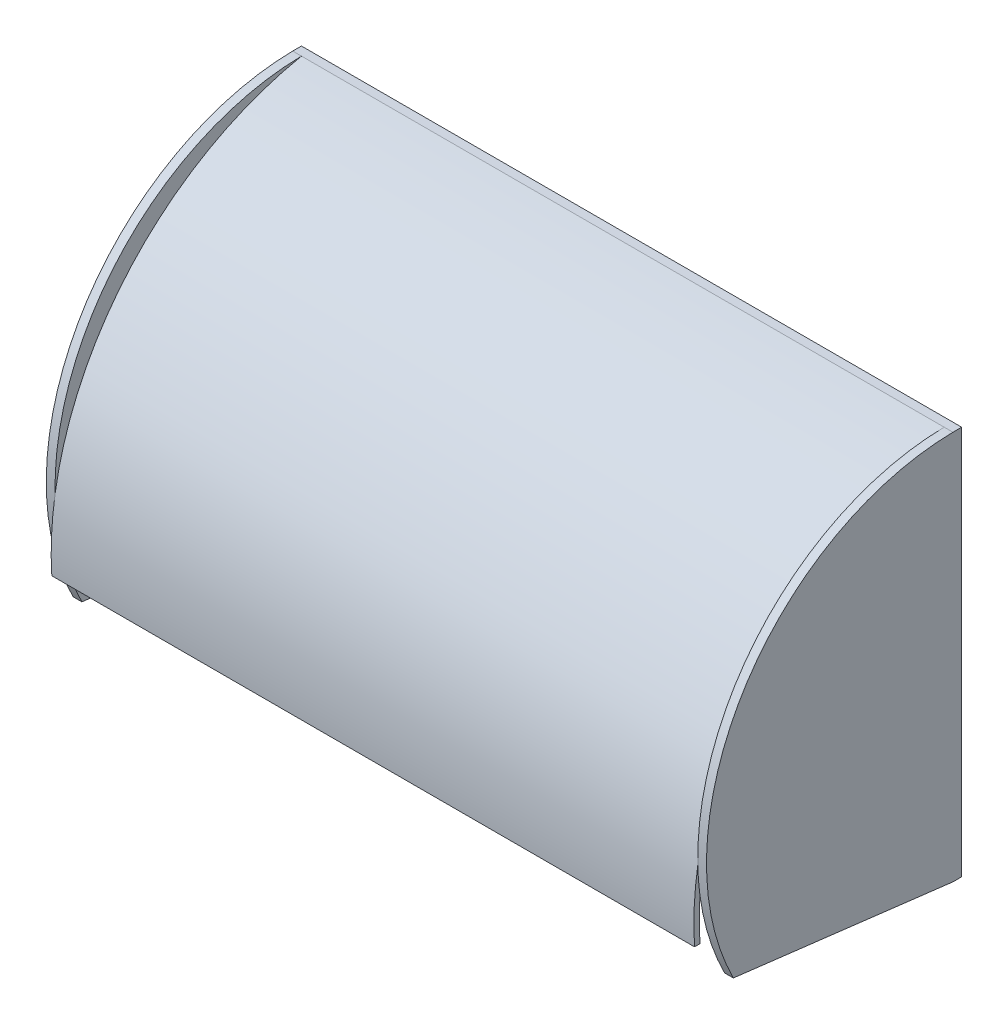
SolidWorks part; units mm, degrees
ref_plane "Front Plane" through (0, 0, 0) normal (0, 0, 1) x (1, 0, 0)
ref_plane "Top Plane" through (0, 0, 0) normal (0, 1, 0) x (1, 0, 0)
ref_plane "Right Plane" through (0, 0, 0) normal (1, 0, 0) x (0, 0, -1)
sketch "Sketch1" plane through (0, 0, 0) normal (0, 0, 1) x (1, 0, 0)
  line L1 (-93.3016, 56.5286) -> (93.3016, 56.5286)
  line L2 (-93.3016, 56.5286) -> (-93.3016, -56.5286)
  line L3 (-93.3016, -56.5286) -> (93.3016, -56.5286)
  line L4 (93.3016, 56.5286) -> (93.3016, -56.5286)
  line L5 (-93.3016, 56.5286) -> (93.3016, -56.5286) construction
  line L6 (-93.3016, -56.5286) -> (93.3016, 56.5286) construction
  point P0 (0, 0)
extrude "Boss-Extrude1" add sketch "Sketch1" along normal blind 2.54
sketch "Sketch2" plane through (-93.3016, 0, 0) normal (-1, 0, 0) x (0, 0, 1)
  line L0 (2.54, 56.5286) -> (2.54, -56.5286) construction
  line L1 (2.54, 56.5286) -> (2.54, 55.3109)
  line L2 (73.4245, -37.8982) -> (75.0178, -37.8982)
  arc A0 (2.54, 56.5286) -> (75.0178, -37.8982) centre (-15.1344, -32.0662) cw
  arc A1 (2.54, 55.3109) -> (73.4245, -37.8982) centre (-15.1792, -31.7224) cw
extrude "Boss-Extrude2" add sketch "Sketch2" against normal up to surface (186.6032 mm away) up to face at (93.3016, 0, 1.27)
sketch "Sketch3" plane through (-93.3016, 0, 0) normal (-1, 0, 0) x (0, 0, 1)
  line L0 (2.54, 56.5286) -> (0, 56.5286)
  line L1 (0, 56.5286) -> (0, -56.5286)
  line L2 (0, -56.5286) -> (2.54, -56.5286)
  line L3 (66.2828, -48.8238) -> (2.54, -56.5286)
  arc A0 (2.54, 56.5286) -> (66.2828, -48.8238) centre (1.4702, -16.0785) cw
extrude "Boss-Extrude3" add sketch "Sketch3" along normal blind 2.54
mirror "Mirror1" about plane through (0, 0, 0) normal (1, 0, 0) of "Boss-Extrude3"
